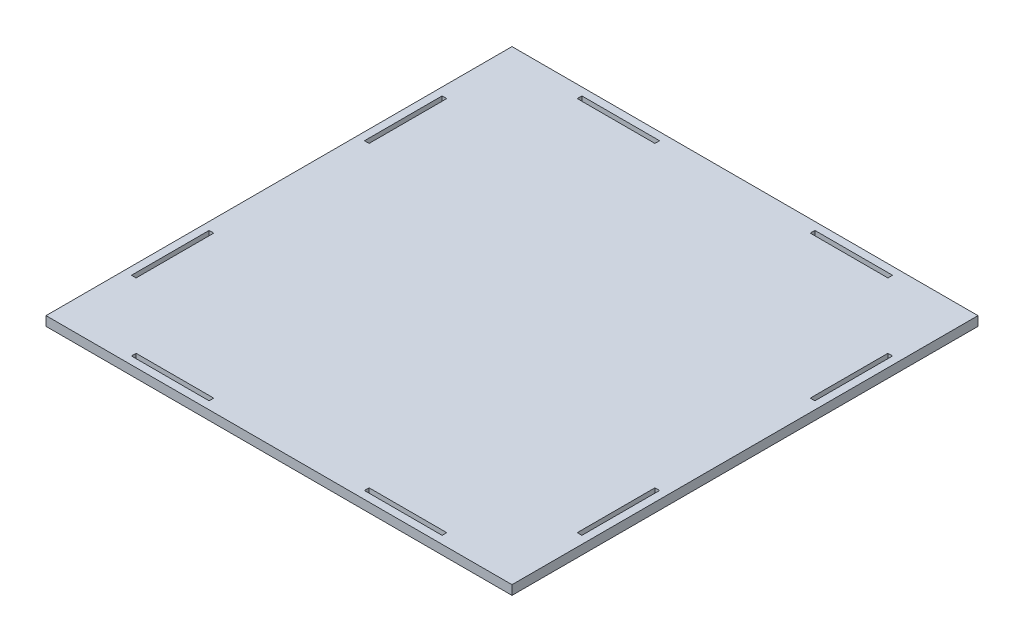
SolidWorks part; units mm, degrees
ref_plane "Front Plane" through (0, 0, 0) normal (0, 0, 1) x (1, 0, 0)
ref_plane "Top Plane" through (0, 0, 0) normal (0, 1, 0) x (1, 0, 0)
ref_plane "Right Plane" through (0, 0, 0) normal (1, 0, 0) x (0, 0, -1)
sketch "Sketch1" plane through (0, 0, 0) normal (0, 1, 0) x (1, 0, 0)
  line L0 (-150, 150) -> (-150, 170) construction
  line L1 (-150, 150) -> (150, 150)
  line L2 (-150, 150) -> (-150, -150)
  line L3 (-150, -150) -> (150, -150)
  line L4 (150, 150) -> (150, -150)
  line L5 (-150, 150) -> (150, -150) construction
  line L6 (-150, -150) -> (150, 150) construction
  line L7 (-150, 170) -> (-100, 170) construction
  line L8 (-100, 170) -> (-100, 185.9399) construction
  line L9 (-100, 185.9399) -> (-50, 185.9399) construction
  line L10 (-50, 185.9399) -> (-50, 170) construction
  line L11 (-50, 170) -> (50, 170) construction
  line L12 (50, 170) -> (50, 185.9399) construction
  line L13 (50, 185.9399) -> (100, 185.9399) construction
  line L14 (100, 185.9399) -> (100, 170) construction
  line L15 (100, 170) -> (150, 170) construction
  line L16 (-150, 150) -> (-182.0377, 150) construction
  line L17 (-182.0377, 150) -> (-182.0377, 145) construction
  line L18 (-100, 145) -> (-50, 145)
  line L19 (-50, 145) -> (-50, 142)
  line L20 (-50, 142) -> (-100, 142)
  line L21 (-100, 142) -> (-100, 145)
  line L22 (50, 145) -> (50, 142)
  line L23 (50, 142) -> (100, 142)
  line L24 (100, 142) -> (100, 145)
  line L25 (100, 145) -> (50, 145)
  line L26 (150, 150) -> (174.1175, 150) construction
  line L27 (174.1175, 150) -> (174.1175, 100) construction
  line L28 (174.1175, 100) -> (194.2868, 100) construction
  line L29 (194.2868, 100) -> (194.2868, 50) construction
  line L30 (194.2868, 50) -> (174.1175, 50) construction
  line L31 (174.1175, 50) -> (174.1175, -50) construction
  line L32 (174.1175, -50) -> (194.2868, -50) construction
  line L33 (194.2868, -50) -> (194.2868, -100) construction
  line L34 (194.2868, -100) -> (174.1175, -100) construction
  line L35 (174.1175, -100) -> (174.1175, -150) construction
  line L36 (174.1175, -150) -> (150, -150) construction
  line L37 (150, -150) -> (150, -155) construction
  line L38 (150, -155) -> (145, -155) construction
  line L39 (145, -100) -> (145, -50)
  line L40 (145, -100) -> (142, -100)
  line L41 (142, -100) -> (142, -50)
  line L42 (142, -50) -> (145, -50)
  line L43 (142, 50) -> (142, 100)
  line L44 (142, 100) -> (145, 100)
  line L45 (145, 100) -> (145, 50)
  line L46 (145, 50) -> (142, 50)
  line L47 (100, -145) -> (100, -142)
  line L48 (100, -142) -> (50, -142)
  line L49 (50, -142) -> (50, -145)
  line L50 (50, -145) -> (100, -145)
  line L51 (-50, -142) -> (-100, -142)
  line L52 (-100, -142) -> (-100, -145)
  line L53 (-100, -145) -> (-50, -145)
  line L54 (-50, -145) -> (-50, -142)
  line L55 (-145, 100) -> (-142, 100)
  line L56 (-142, 100) -> (-142, 50)
  line L57 (-142, 50) -> (-145, 50)
  line L58 (-145, 50) -> (-145, 100)
  line L59 (-142, -50) -> (-145, -50)
  line L60 (-145, -50) -> (-145, -100)
  line L61 (-145, -100) -> (-142, -100)
  line L62 (-142, -100) -> (-142, -50)
  point P0 (0, 0)
extrude "Boss-Extrude1" add sketch "Sketch1" along normal blind 6
